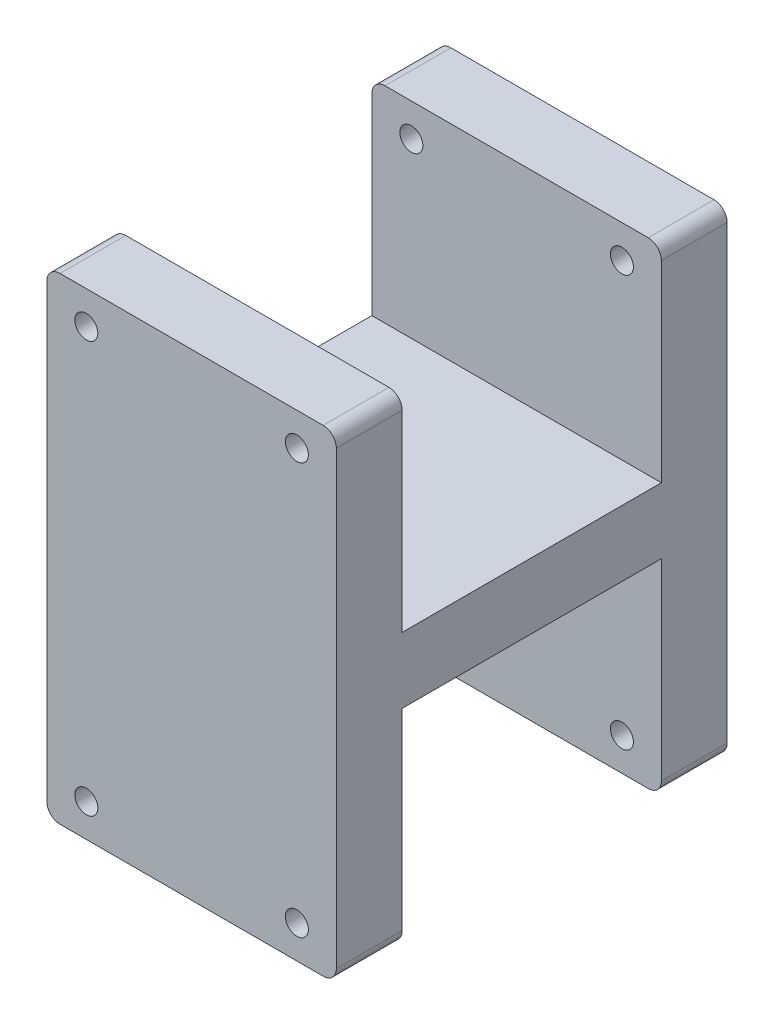
SolidWorks part; units mm, degrees
ref_plane "正面" through (0, 0, 0) normal (0, 0, 1) x (1, 0, 0)
ref_plane "平面" through (0, 0, 0) normal (0, 1, 0) x (1, 0, 0)
ref_plane "右側面" through (0, 0, 0) normal (1, 0, 0) x (0, 0, -1)
sketch "ｽｹｯﾁ2" plane through (0, 0, 0) normal (0, 0, 1) x (1, 0, 0)
  line L1 (22, -36.25) -> (-22, -36.25)
  line L2 (22, -36.25) -> (22, 36.25)
  line L3 (22, 36.25) -> (-22, 36.25)
  line L4 (-22, -36.25) -> (-22, 36.25)
  line L5 (22, -36.25) -> (-22, 36.25) construction
  line L6 (22, 36.25) -> (-22, -36.25) construction
  point P0 (0, 0)
  dimension "D1" = 72.5
  dimension "D2" = 44
extrude "ﾎﾞｽ - 押し出し1" add sketch "ｽｹｯﾁ2" along normal blind 59.4
sketch "ｽｹｯﾁ3" plane through (0, 0, 59.4) normal (0, 0, 1) x (1, 0, 0)
  line L0 (0, -36.25) -> (0, 36.25)
  line L1 (22, 36.25) -> (-22, 36.25) construction
  line L2 (0, 36.25) -> (0, 0)
  line L3 (0, 0) -> (22, 0)
  line L4 (22, -36.25) -> (22, 36.25) construction
  circle A0 centre (-16, 31.25) radius 1.75
  circle A1 centre (16, 31.25) radius 1.75
  circle A2 centre (16, -31.25) radius 1.75
  circle A3 centre (-16, -31.25) radius 1.75
  point P8 (0, 0)
  dimension "D1" = 3.5
  dimension "D2" = 16
  dimension "D3" = 31.25
extrude "ｶｯﾄ - 押し出し1" cut sketch "ｽｹｯﾁ3" against normal through all contours A0 | A1 | A2 | A3
sketch "ｽｹｯﾁ4" plane through (22, 0, 0) normal (1, 0, 0) x (0, 0, -1)
  line L0 (-59.4, -36.25) -> (0, -36.25) construction
  line L1 (-10, -5) -> (-49.4, -5)
  line L2 (-10, -5) -> (-10, -36.25)
  line L3 (-10, -36.25) -> (-49.4, -36.25)
  line L4 (-49.4, -5) -> (-49.4, -36.25)
  line L5 (-10, -5) -> (-49.4, -36.25) construction
  line L6 (-10, -36.25) -> (-49.4, -5) construction
  line L8 (0, 0) -> (-59.4, 0)
  line L9 (-10, 36.25) -> (-49.4, 5) construction
  line L10 (-10, 5) -> (-49.4, 36.25) construction
  line L11 (-49.4, 5) -> (-49.4, 36.25)
  line L12 (-10, 36.25) -> (-49.4, 36.25)
  line L13 (-10, 5) -> (-10, 36.25)
  line L14 (-59.4, -36.25) -> (-59.4, 36.25) construction
  line L15 (0, -36.25) -> (0, 36.25) construction
  line L16 (-10, 5) -> (-49.4, 5)
  point P0 (-29.7, -20.625)
  point P10 (-29.7, 0)
  point P18 (-29.7, 20.625)
  line M9 (0, 36.25) -> (-59.4, 36.25)
  line M11 (-59.4, -36.25) -> (0, -36.25)
  dimension "D1" = 10
  dimension "D2" = 5
  dimension "D3" = 10
extrude "ｶｯﾄ - 押し出し2" cut sketch "ｽｹｯﾁ4" against normal through all contours L1 L4 L2 M11 | L16 L13 L11 M9
fillet "ﾌｨﾚｯﾄ1" radius 2 8 edges at (-22, -36.25, 5) (-22, -36.25, 54.4) (-22, 36.25, 54.4) (-22, 36.25, 5) (22, 36.25, 5) (22, 36.25, 54.4) (22, -36.25, 5) (22, -36.25, 54.4)
